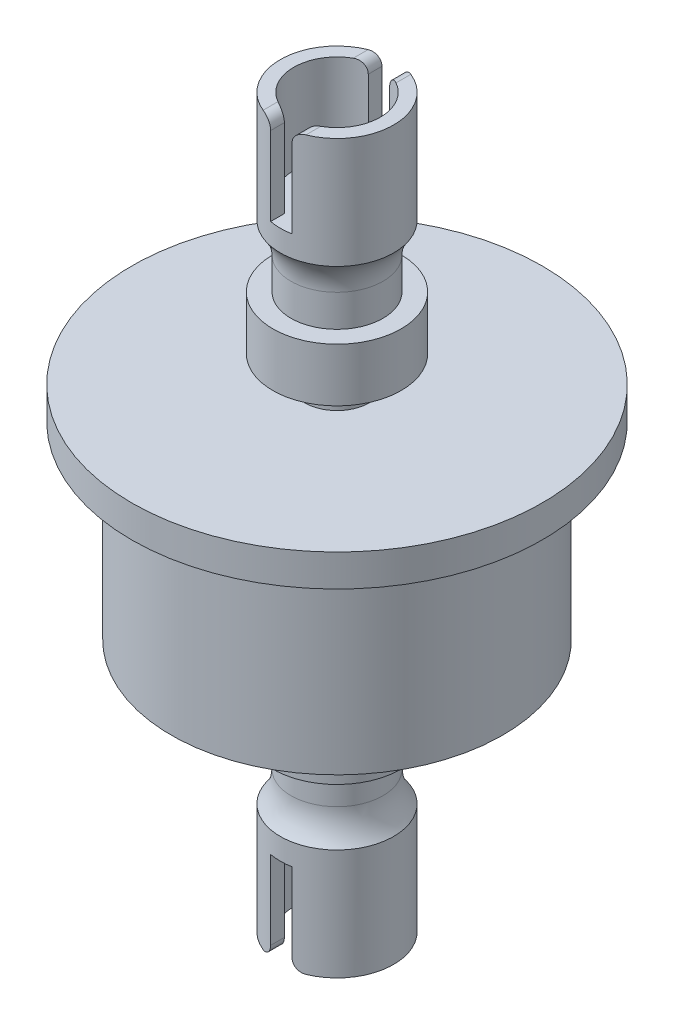
SolidWorks part; units mm, degrees
ref_plane "Front Plane" through (0, 0, 0) normal (0, 0, 1) x (1, 0, 0)
ref_plane "Top Plane" through (0, 0, 0) normal (0, 1, 0) x (1, 0, 0)
ref_plane "Right Plane" through (0, 0, 0) normal (1, 0, 0) x (0, 0, -1)
sketch "Sketch1" plane through (0, 0, 0) normal (0, 0, 1) x (1, 0, 0)
  line L0 (0, 0) -> (0, 68)
  line L1 (0, 32.5) -> (-15.5, 32.5) construction
  line L2 (0, 21.1667) -> (-6, 21.1667)
  line L3 (0, 41.3333) -> (-15.5, 41.3333)
  line L4 (0, 23.6667) -> (-15.5, 23.6667)
  line L5 (0, 16.1667) -> (-6, 16.1667)
  line L6 (0, 44.3333) -> (-19.2, 44.3333)
  line L7 (-15.5, 41.3333) -> (-15.5, 23.6667)
  line L8 (-6, 21.1667) -> (-6, 16.1667)
  line L9 (-3, 23.6667) -> (-3, 21.1667)
  line L10 (0, 51.8333) -> (-6, 51.8333)
  line L11 (-6, 46.8333) -> (-6, 51.8333)
  line L12 (-3, 44.3333) -> (-3, 46.8333)
  line L13 (0, 46.8333) -> (-6, 46.8333)
  line L14 (-4.3, 51.8333) -> (-4.3, 54.8333)
  line L15 (-19.2, 44.3333) -> (-19.2, 41.3333)
  line L16 (-15.5, 34) -> (0, 34) construction
  line L17 (-5.3, 57.6333) -> (-5.3, 68)
  line L18 (-5.3, 68) -> (-2, 68)
  line L19 (-1, 67) -> (-1, 59.6333)
  line L20 (-1, 59.6333) -> (0, 59.6333)
  line L21 (-4.3, 16.1667) -> (-4.3, 13.1667)
  line L22 (-5.3, 10.3667) -> (-5.3, 0)
  line L23 (-1, 8.3667) -> (0, 8.3667)
  line L24 (-1, 1) -> (-1, 8.3667)
  line L25 (-5.3, 0) -> (-2, 0)
  line L26 (-3, 44.3333) -> (-3, 41.3333)
  line L27 (-19.2, 41.3333) -> (-15.5, 41.3333)
  arc A0 (-4.3, 54.8333) -> (-5.3, 57.6333) centre (-8.72, 54.8333) ccw
  arc A1 (-2, 68) -> (-1, 67) centre (-2, 67) cw
  arc A2 (-4.3, 13.1667) -> (-5.3, 10.3667) centre (-8.72, 13.1667) cw
  arc A3 (-2, 0) -> (-1, 1) centre (-2, 1) ccw
  point P19 (-15.5, 34)
  point P26 (0, 34)
  dimension "D14" = 1
  dimension "D1" = 68
  dimension "D2" = 15.5
  dimension "D3" = 6
  dimension "D4" = 8.8333
  dimension "D5" = 2.5
  dimension "D6" = 5
  dimension "D7" = 3
  dimension "D8" = 3
  dimension "D9" = 4.3
  dimension "D10" = 1
  dimension "D11" = 3
  dimension "D12" = 2.8
  dimension "D13" = 1
  dimension "D15" = 2
  dimension "D16" = 19.2
  dimension "D17" = 2.5
revolve "Revolve1" add sketch "Sketch1" angle 360 about L0
sketch "Sketch2" plane through (0, 0, 0) normal (0, 0, 1) x (1, 0, 0)
  line L0 (-1, 1) -> (-1, 8.3667) construction
  line L1 (0, 0) -> (0, 68) construction
  line L2 (-1, 59.6333) -> (0, 59.6333) construction
  line L3 (-1, 67) -> (-1, 59.6333) construction
  line L4 (-1, 1) -> (-1, 8.3667)
  line L5 (0, 0) -> (0, 68)
  line L6 (-1, 59.6333) -> (1, 59.6333)
  line L7 (-1, 67) -> (-1, 59.6333)
  line L8 (-1, 8.3667) -> (0, 8.3667) construction
  line L9 (-1, 8.3667) -> (1, 8.3667)
  line L10 (1, 67) -> (1, 59.6333)
  line L11 (1, 1) -> (1, 8.3667)
  line L12 (-2, 68) -> (2, 68)
  line L13 (-2, 0) -> (2, 0)
  arc A0 (-2, 0) -> (-1, 1) centre (-2, 1) ccw construction
  arc A1 (-1, 67) -> (-2, 68) centre (-2, 67) ccw construction
  arc A2 (-2, 0) -> (-1, 1) centre (-2, 1) ccw
  arc A3 (-1, 67) -> (-2, 68) centre (-2, 67) ccw
  arc A4 (1, 67) -> (2, 68) centre (2, 67) cw
  arc A5 (2, 0) -> (1, 1) centre (2, 1) cw
  point P0 (0, 8.3667)
extrude "Cut-Extrude1" cut sketch "Sketch2" against normal through all and the other way through all contours L13 A5 L11 L9 L5 | A2 L13 L5 L9 L4 | L7 L6 L10 A4 L12 A3
sketch "Sketch3" plane through (0, 68, 0) normal (0, 1, 0) x (1, 0, 0)
  circle A0 centre (0, 0) radius 4.05
  arc A1 (-2, 4.9082) -> (-2, -4.9082) centre (0, 0) ccw construction
  dimension "D1" = 1.25
extrude "Cut-Extrude2" cut sketch "Sketch3" against normal up to surface (8.3667 mm away) up to face at (0, 59.6333, 0)
sketch "Sketch4" plane through (0, 0, 0) normal (0, -1, 0) x (1, 0, 0)
  circle A0 centre (0, 0) radius 4.05
  circle A1 centre (0, 0) radius 5.3 construction
  dimension "D1" = 1.25
extrude "Cut-Extrude3" cut sketch "Sketch4" against normal up to surface (8.3667 mm away) up to face at (0, 8.3667, 0)
